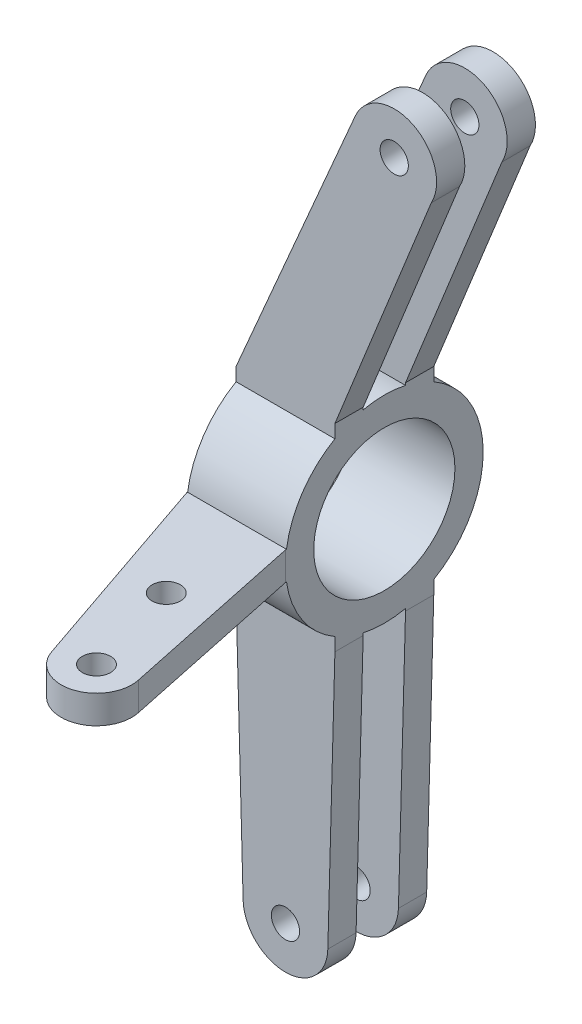
SolidWorks part; units mm, degrees
ref_plane "Front Plane" through (0, 0, 0) normal (0, 0, 1) x (1, 0, 0)
ref_plane "Top Plane" through (0, 0, 0) normal (0, 1, 0) x (1, 0, 0)
ref_plane "Right Plane" through (0, 0, 0) normal (1, 0, 0) x (0, 0, -1)
sketch "Sketch1" plane through (0, 0, 0) normal (1, 0, 0) x (0, 0, -1)
  circle A0 centre (0, 0) radius 25
  circle A1 centre (0, 0) radius 35
  dimension "D1" = 50
  dimension "D2" = 70
extrude "Boss-Extrude1" add sketch "Sketch1" along normal mid plane 35
sketch "Sketch2" plane through (0, 0, 0) normal (0, 0, 1) x (1, 0, 0)
  line L0 (0, 35) -> (38.5, 127) construction
  line L2 (0, -35) -> (0, -127) construction
  line L4 (0, -127) -> (38.5, 127) construction
  line L6 (-17.5, 35) -> (24.7257, 132.9387)
  line L7 (17.5, 35) -> (-17.5, 35) construction
  line L8 (-17.5, 35) -> (17.5, 35)
  line L10 (-17.5, 35) -> (-17.5, -35) construction
  line L11 (17.5, -35) -> (14.9945, -127.4066)
  line L12 (-17.5, -35) -> (-14.9945, -127.4066)
  line L13 (-17.5, -35) -> (17.5, -35) construction
  line L14 (-17.5, -35) -> (17.5, -35)
  line L15 (51.6092, 119.7096) -> (17.5, 35)
  circle A0 centre (38.5, 127) radius 5
  arc A2 (51.6092, 119.7096) -> (24.7257, 132.9387) centre (38.5, 127) ccw
  circle A3 centre (0, -127) radius 5
  arc A4 (-14.9945, -127.4066) -> (14.9945, -127.4066) centre (0, -127) ccw
  dimension "D4" = 10
  dimension "D5" = 203.323
  dimension "D6" = 15
  dimension "D8" = 30
  dimension "D9" = 10
  dimension "D2" = 127
  dimension "D3" = 127
  dimension "D7" = 84.7096
ref_plane "Plane1" through (0, 0, 7.5) normal (0, 0, 1) x (1, 0, 0)
sketch "Sketch4" plane through (0, 0, 7.5) normal (0, 0, 1) x (1, 0, 0)
  line L0 (-17.5, -35) -> (-14.9945, -127.4066) construction
  line L1 (17.5, -35) -> (14.9945, -127.4066) construction
  line L2 (-17.5, -35) -> (17.5, -35) construction
  line L5 (-17.5, 35) -> (24.7257, 132.9387) construction
  line L6 (-17.5, -35) -> (-14.9945, -127.4066)
  line L7 (17.5, -35) -> (14.9945, -127.4066)
  line L8 (-17.5, -35) -> (17.5, -35)
  line L11 (-17.5, 35) -> (24.7257, 132.9387)
  line L12 (-17.5, 35) -> (17.5, 35)
  line L14 (17.5, 35) -> (51.6092, 119.7096)
  circle A0 centre (0, -127) radius 5 construction
  arc A1 (-14.9945, -127.4066) -> (14.9945, -127.4066) centre (0, -127) ccw construction
  circle A2 centre (38.5, 127) radius 5 construction
  circle A4 centre (0, -127) radius 5
  arc A5 (-14.9945, -127.4066) -> (14.9945, -127.4066) centre (0, -127) ccw
  circle A6 centre (38.5, 127) radius 5
  arc A8 (51.6092, 119.7096) -> (24.7257, 132.9387) centre (38.5, 127) ccw
ref_plane "Plane2" through (0, 0, -7.5) normal (0, 0, 1) x (1, 0, 0)
sketch "Sketch5" plane through (0, 0, -7.5) normal (0, 0, 1) x (1, 0, 0)
  line L0 (-17.5, -35) -> (-14.9945, -127.4066) construction
  line L1 (17.5, -35) -> (14.9945, -127.4066) construction
  line L2 (-17.5, -35) -> (17.5, -35) construction
  line L3 (-17.5, 35) -> (17.5, 35) construction
  line L5 (-17.5, 35) -> (24.7257, 132.9387) construction
  line L6 (-17.5, -35) -> (-14.9945, -127.4066)
  line L7 (17.5, -35) -> (14.9945, -127.4066)
  line L8 (-17.5, -35) -> (17.5, -35)
  line L9 (-17.5, 35) -> (17.5, 35)
  line L11 (-17.5, 35) -> (24.7257, 132.9387)
  line L12 (17.5, 35) -> (51.6092, 119.7096)
  circle A0 centre (0, -127) radius 5 construction
  arc A1 (-14.9945, -127.4066) -> (14.9945, -127.4066) centre (0, -127) ccw construction
  circle A2 centre (38.5, 127) radius 5 construction
  arc A3 (51.6092, 119.7096) -> (24.7257, 132.9387) centre (38.5, 127) ccw construction
  circle A4 centre (0, -127) radius 5
  arc A5 (-14.9945, -127.4066) -> (14.9945, -127.4066) centre (0, -127) ccw
  circle A6 centre (38.5, 127) radius 5
  arc A7 (51.6092, 119.7096) -> (24.7257, 132.9387) centre (38.5, 127) ccw
extrude "Boss-Extrude3" add sketch "Sketch5" against normal blind 10 separate body
extrude "Boss-Extrude5" add sketch "Sketch4" along normal blind 10 separate body
sketch "Sketch7" plane through (17.5, 0, 0) normal (1, 0, 0) x (0, 0, -1)
  line L0 (-17.5, 35) -> (-17.5, 30.3109)
  line L1 (-7.5, 35) -> (-7.5, 34.187)
  line L2 (-17.5, 35) -> (-7.5, 35)
  line L3 (7.5, 35) -> (7.5, 34.187)
  line L7 (7.5, -35) -> (7.5, -34.187)
  line L8 (7.5, -35) -> (17.5, -35)
  line L9 (17.5, -35) -> (17.5, -30.3109)
  line L10 (-7.5, -35) -> (-7.5, -34.187)
  line L11 (-7.5, -35) -> (-17.5, -35)
  line L14 (7.5, 35) -> (17.5, 35)
  line L15 (17.5, 35) -> (17.5, 30.3109)
  line L16 (-17.5, -35) -> (-17.5, -30.3109)
  circle A0 centre (0, 0) radius 35 construction
  arc A1 (-17.5, -30.3109) -> (-7.5, -34.187) centre (0, 0) ccw
  arc A2 (-7.5, 34.187) -> (-17.5, 30.3109) centre (0, 0) ccw
  arc A3 (17.5, 30.3109) -> (7.5, 34.187) centre (0, 0) ccw
  arc A4 (7.5, -34.187) -> (17.5, -30.3109) centre (0, 0) ccw
extrude "Boss-Extrude6" add sketch "Sketch7" against normal up to surface (35 mm away) up to face at (-17.5, 0, -35)
sketch "Sketch14" plane through (0, 0, 0) normal (0, 1, 0) x (1, 0, 0)
  line L0 (0, -35) -> (0, -84.7871) construction
  line L1 (-17.5, -35) -> (17.5, -35) construction
  line L2 (0, -35) -> (19.1608, -103.58) construction
  line L3 (17.5, -35) -> (31.3928, -101.0054)
  line L4 (17.5, -35) -> (-17.5, -35)
  line L5 (-17.5, -35) -> (7.3331, -107.6243)
  circle A0 centre (19.1608, -103.58) radius 5
  arc A1 (7.3331, -107.6243) -> (31.3928, -101.0054) centre (19.1608, -103.58) ccw
  circle A2 centre (9.5804, -69.29) radius 5
  dimension "D2" = 10
  dimension "D3" = 25
  dimension "D5" = 10
  dimension "D1" = 15.61
  dimension "D4" = 68.58
extrude "Boss-Extrude12" add sketch "Sketch14" along normal mid plane 10 separate body
sketch "Sketch15" plane through (17.5, 0, 0) normal (1, 0, 0) x (0, 0, -1)
  line L0 (-35, -5) -> (-35, 5)
  line L1 (-101.0054, 5) -> (-35, 5) construction
  line L2 (-35, 5) -> (-35, -5) construction
  line L3 (-35, 5) -> (-34.641, 5)
  line L4 (-34.641, 5) -> (-35, 0)
  line L5 (-35, 0) -> (-34.641, -5)
  line L6 (-34.641, -5) -> (-35, -5)
  arc A0 (-17.5, 30.3109) -> (-17.5, -30.3109) centre (0, 0) ccw construction
  arc M5 (-17.5, 30.3109) -> (-17.5, -30.3109) centre (0, 0) ccw
extrude "Boss-Extrude13" add sketch "Sketch15" against normal up to surface (35 mm away) contours L6 L0 M5 | L3 L0 M5 up to face at (-17.5, 0, 0)
